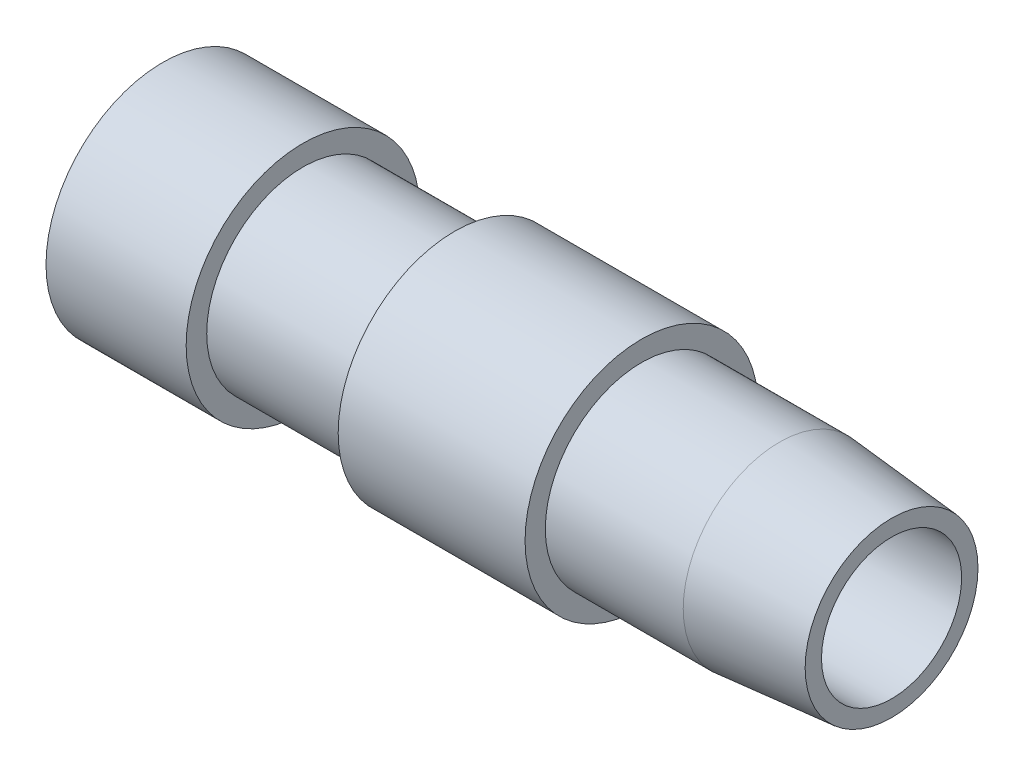
SolidWorks part; units mm, degrees
material "6061-T6 (SS)"
ref_plane "Front Plane" through (0, 0, 0) normal (0, 0, 1) x (1, 0, 0)
ref_plane "Top Plane" through (0, 0, 0) normal (0, 1, 0) x (1, 0, 0)
ref_plane "Right Plane" through (0, 0, 0) normal (1, 0, 0) x (0, 0, -1)
sketch "Sketch1" plane through (0, 0, 0) normal (0, 0, 1) x (1, 0, 0)
  line L0 (0, 4.7625) -> (0, 7.9375)
  line L1 (0, 7.9375) -> (9.525, 7.9375)
  line L2 (9.525, 7.9375) -> (9.525, 6.5405)
  line L3 (9.525, 6.5405) -> (19.8374, 6.5405)
  line L4 (19.8374, 6.5405) -> (19.8374, 7.9172)
  line L5 (19.8374, 7.9172) -> (32.5374, 7.9172)
  line L6 (32.5374, 7.9172) -> (32.5374, 6.5405)
  line L7 (32.5374, 6.5405) -> (41.91, 6.5405)
  line L8 (41.91, 6.5405) -> (49.53, 5.8738)
  line L9 (49.53, 5.8738) -> (49.53, 4.7625)
  line L10 (49.53, 4.7625) -> (0, 4.7625)
  line L11 (0, 0) -> (19.8374, 0) construction
  point P0 (0, 6.35)
  dimension "D1" = 49.53
  dimension "D2" = 12.7
  dimension "D3" = 16.9926
  dimension "D4" = 4.7625
  dimension "D5" = 7.9375
  dimension "D6" = 5
  dimension ".43" = 6.5405
  dimension "D7" = 7.62
  dimension "D8" = 9.525
  dimension "D9" = 7.9172
revolve "Revolve1" add sketch "Sketch1" angle 360 about L11
sketch "Sketch2" plane through (0, 0, 0) normal (-1, 0, 0) x (0, 0, 1)
  line L1 (-0.7938, -6.985) -> (0.7937, -6.985)
  line L2 (-0.7938, -6.985) -> (-0.7938, 6.985)
  line L3 (-0.7938, 6.985) -> (0.7937, 6.985)
  line L4 (0.7937, -6.985) -> (0.7937, 6.985)
  line L5 (-0.7938, -6.985) -> (0.7937, 6.985) construction
  line L6 (-0.7938, 6.985) -> (0.7937, -6.985) construction
  point P0 (0, 0)
  dimension "D1" = 1.5875
  dimension "D2" = 13.97
extrude "Cut-Extrude1" cut sketch "Sketch2" against normal blind 3.175
